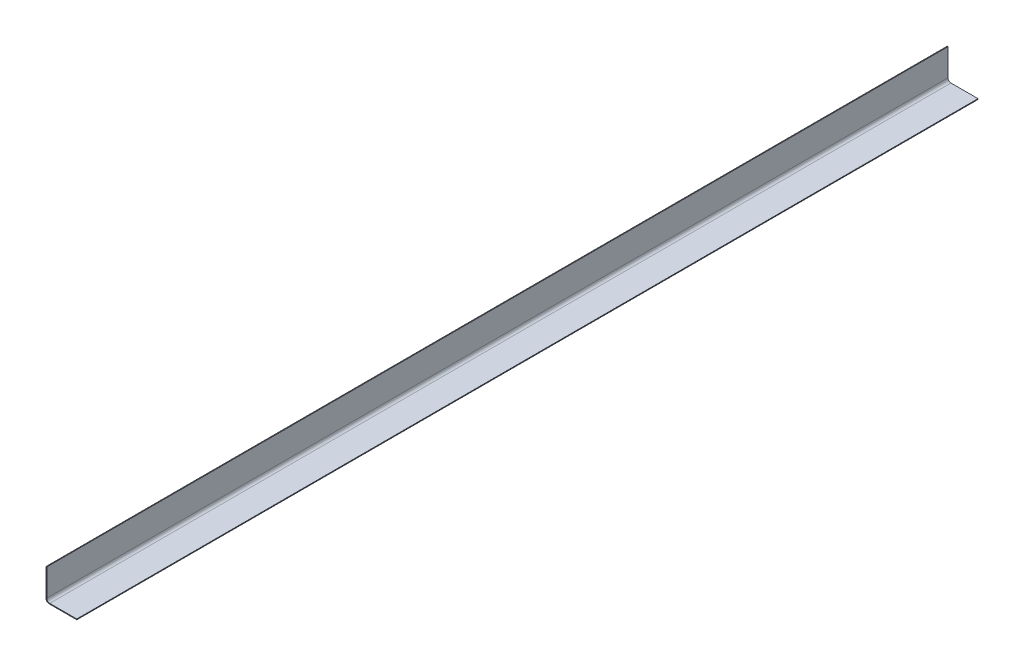
SolidWorks part; units mm, degrees
ref_plane "Front Plane" through (0, 0, 0) normal (0, 0, 1) x (1, 0, 0)
ref_plane "Top Plane" through (0, 0, 0) normal (0, 1, 0) x (1, 0, 0)
ref_plane "Right Plane" through (0, 0, 0) normal (1, 0, 0) x (0, 0, -1)
sketch "Sketch1" plane through (0, 0, 0) normal (0, 0, 1) x (1, 0, 0)
  line L0 (4, 0) -> (40, 0)
  line L1 (40, 0) -> (40, -1)
  line L2 (40, -1) -> (3, -1)
  line L3 (-1, 3) -> (-1, 40)
  line L4 (-1, 40) -> (0, 40)
  line L5 (0, 40) -> (0, 4)
  arc A0 (-1, 3) -> (3, -1) centre (3, 3) ccw
  arc A1 (4, 0) -> (0, 4) centre (4, 4) cw
  point P11 (0, 0)
  dimension "D5" = 4
  dimension "D1" = 40
  dimension "D2" = 40
  dimension "D3" = 1
  dimension "D4" = 1
extrude "Boss-Extrude1" add sketch "Sketch1" along normal blind 1200
